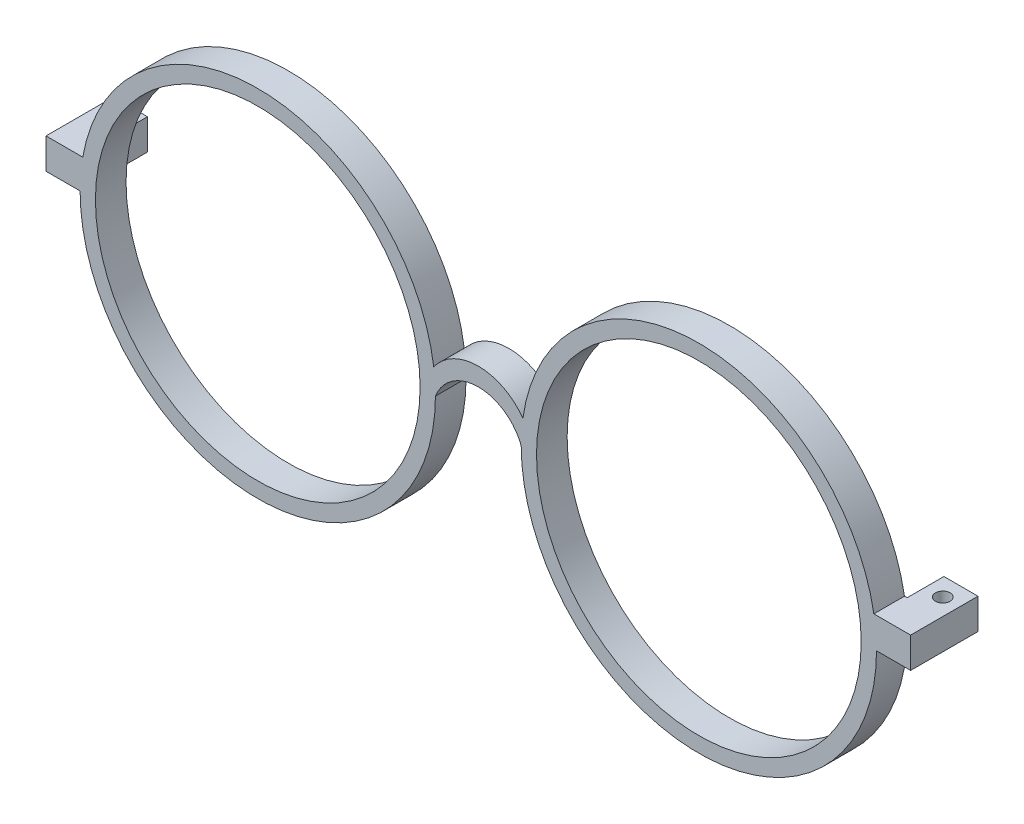
SolidWorks part; units mm, degrees
ref_plane "Ebene vorne" through (0, 0, 0) normal (0, 0, 1) x (1, 0, 0)
ref_plane "Ebene oben" through (0, 0, 0) normal (0, 1, 0) x (1, 0, 0)
ref_plane "Ebene rechts" through (0, 0, 0) normal (1, 0, 0) x (0, 0, -1)
sketch "Skizze1" plane through (0, 0, 0) normal (0, 0, 1) x (1, 0, 0)
  line L0 (65, 0) -> (70.5657, 0)
  line L1 (70.5657, 0) -> (70.5657, 5)
  line L2 (70.5657, 5) -> (64.5657, 5)
  line L3 (-65, 0) -> (-70.5657, 0)
  line L4 (-70.5657, 0) -> (-70.5657, 5)
  line L5 (-70.5657, 5) -> (-64.5657, 5)
  circle A0 centre (-36, 0) radius 29
  circle A1 centre (36, 0) radius 29
  arc A2 (-7, 0) -> (7, 0) centre (0, -2.6926) cw
  circle A3 centre (36, 0) radius 26.5
  circle A4 centre (-36, 0) radius 26.5
  arc A5 (-7.2759, 3.9905) -> (7.2772, 4) centre (0.0041, -1.1921) cw
  dimension "D1" = 58
  dimension "D2" = 58
  dimension "D5" = 7.5
  dimension "D6" = 53
  dimension "D7" = 53
  dimension "D3" = 36
  dimension "D4" = 36
  dimension "D8" = 4
  dimension "D9" = 4
  dimension "D10" = 5
  dimension "D11" = 5
  dimension "D12" = 6
  dimension "D13" = 6
extrude "Aufsatz-Linear austragen1" add sketch "Skizze1" along normal blind 5 contours A0 A4 | A0 L5 L4 L3 | A4 | A5 A0 A2 A1 | A1 A3 | A1 L0 L1 L2
sketch "Skizze2" plane through (0, 0, 0) normal (0, 0, -1) x (-1, 0, 0)
  line L1 (-70.5657, 5) -> (-65, 5)
  line L2 (-70.5657, 5) -> (-70.5657, 0)
  line L3 (-70.5657, 0) -> (-65, 0)
  line L4 (-65, 5) -> (-65, 0)
  line L5 (70.5657, 5) -> (65, 5)
  line L6 (70.5657, 5) -> (70.5657, 0)
  line L7 (70.5657, 0) -> (65, 0)
  line L8 (65, 5) -> (65, 0)
extrude "Aufsatz-Linear austragen2" add sketch "Skizze2" along normal blind 6
hole_wizard "Durchgangsloch für M21" positions "Skizze4" profile "Skizze3" hole size "M2" standard "ANSI Metrisch" end condition through all
sketch "Skizze4" plane through (0, 5, 0) normal (0, 1, 0) x (1, 0, 0)
  line L0 (65, 6) -> (70.5657, 6) construction
  line L1 (70.5657, -5) -> (70.5657, 6) construction
  line L2 (-70.5657, 6) -> (-65, 6) construction
  line L3 (-70.5657, -5) -> (-70.5657, 6) construction
  point P0 (-67.8157, 3)
  point P2 (67.8157, 3)
  dimension "D1" = 3
  dimension "D2" = 2.75
  dimension "D3" = 3
  dimension "D4" = 2.75
sketch "Skizze3" plane through (-67.8157, 5, -3) normal (1, 0, 0) x (0, 0, 1)
  line L0 (0, 0) -> (0, 34)
  line L1 (0, 34) -> (1.2, 34)
  line L2 (1.2, 34) -> (1.2, 0)
  line L5 (1.2, 0) -> (0, 0)
  line L11 (0, -6.35) -> (0, 107.95) construction
  dimension "Bohrerdurchmesser" = 2.4
  dimension "Bohrungstiefe" = 34
